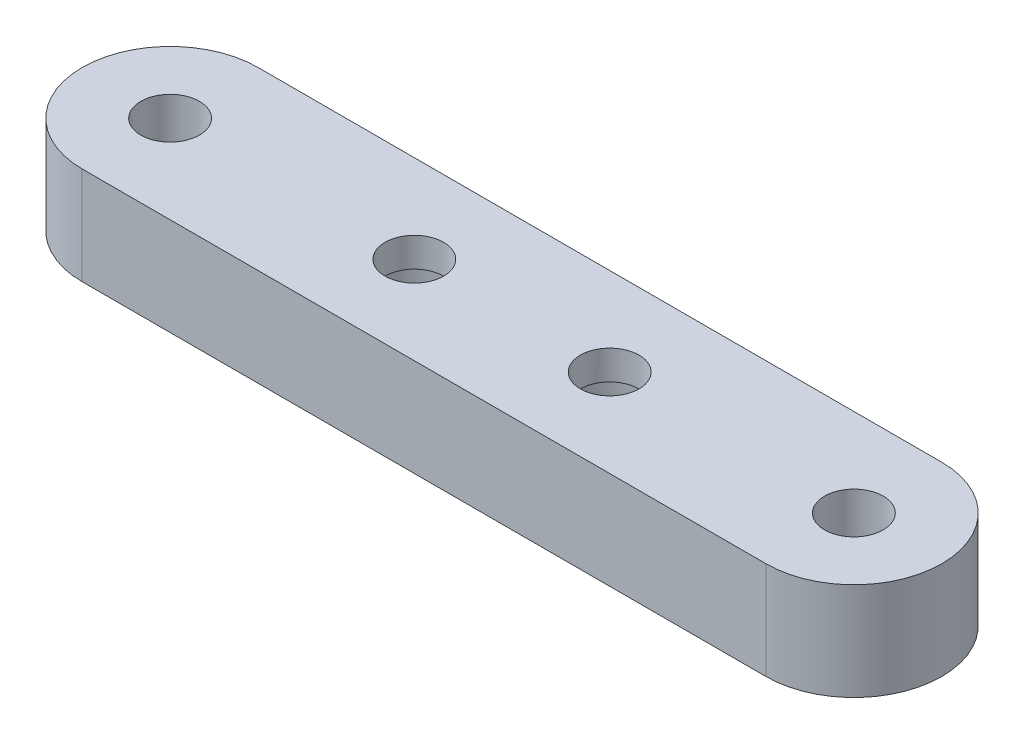
SolidWorks part; units mm, degrees
material "6061 Alloy"
ref_plane "Front Plane" through (0, 0, 0) normal (0, 0, 1) x (1, 0, 0)
ref_plane "Top Plane" through (0, 0, 0) normal (0, 1, 0) x (1, 0, 0)
ref_plane "Right Plane" through (0, 0, 0) normal (1, 0, 0) x (0, 0, -1)
sketch "Sketch2" plane through (0, 0, 0) normal (0, 1, 0) x (1, 0, 0)
  line L0 (25, 0) -> (25, 9)
  line L1 (25, 9) -> (-45, 9)
  line L2 (-45, -9) -> (25, -9)
  circle A4 centre (-45, 0) radius 3
  circle A5 centre (-20, 0) radius 3
  circle A6 centre (0, 0) radius 3
  circle A7 centre (25, 0) radius 3
  circle A8 centre (-45, 0) radius 9
  circle A9 centre (25, 0) radius 9
  dimension "D1" = 25
  dimension "D2" = 20
  dimension "D3" = 25
extrude "Boss-Extrude1" add sketch "Sketch2" along normal blind 10
sketch "Sketch3" plane through (0, 0, 0) normal (0, -1, 0) x (1, 0, 0)
  circle A0 centre (-20, 0) radius 5
  circle A1 centre (0, 0) radius 5
extrude "Cut-Extrude1" cut sketch "Sketch3" against normal blind 7
